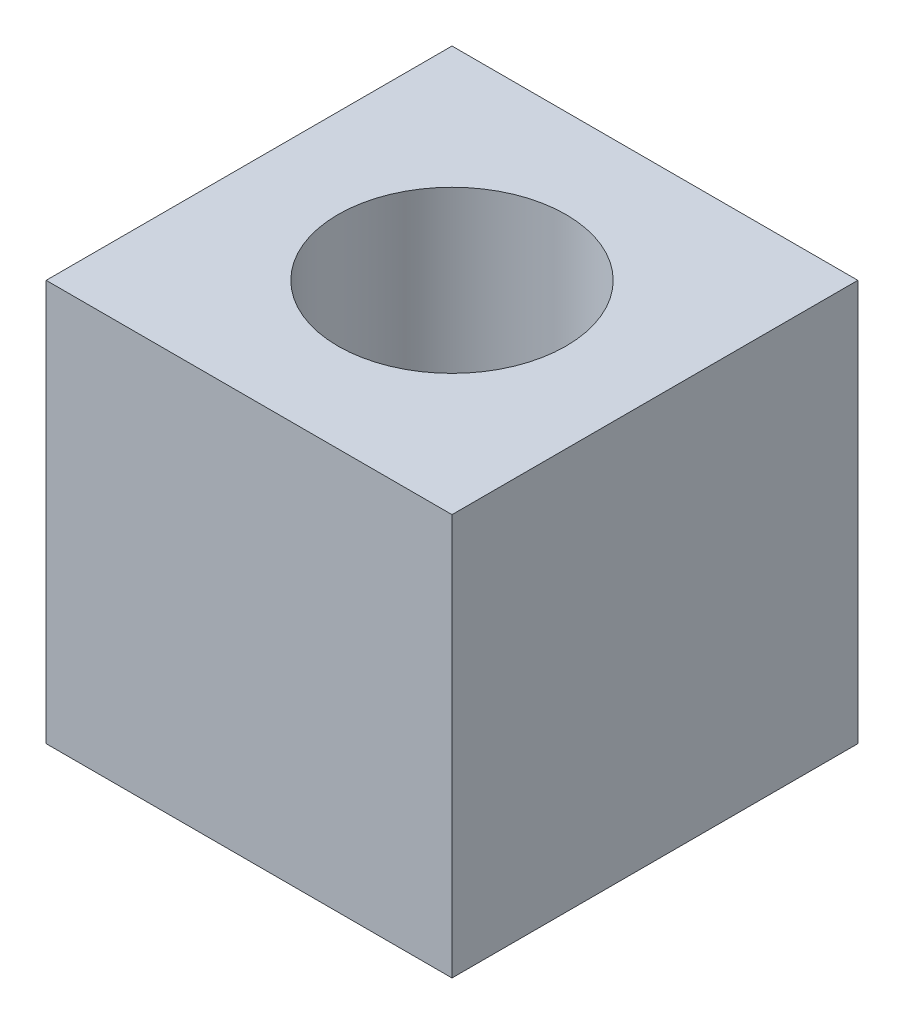
SolidWorks part; units mm, degrees
ref_plane "Front Plane" through (0, 0, 0) normal (0, 0, 1) x (1, 0, 0)
ref_plane "Top Plane" through (0, 0, 0) normal (0, 1, 0) x (1, 0, 0)
ref_plane "Right Plane" through (0, 0, 0) normal (1, 0, 0) x (0, 0, -1)
sketch "Sketch1" plane through (0, 0, 0) normal (0, 1, 0) x (1, 0, 0)
  line L0 (5.6515, 11.303) -> (5.6515, 0) construction
  line L1 (0, 0) -> (11.303, 0)
  line L2 (0, 0) -> (0, 11.303)
  line L3 (0, 11.303) -> (11.303, 11.303)
  line L4 (11.303, 0) -> (11.303, 11.303)
  line L5 (0, 5.6515) -> (11.303, 5.6515) construction
  circle A0 centre (5.6515, 5.6515) radius 3.175
  dimension "D3" = 6.35
  dimension "D1" = 11.303
  dimension "D2" = 11.303
extrude "Boss-Extrude1" add sketch "Sketch1" along normal blind 11.176
sketch "Sketch2" plane through (0, 11.176, 0) normal (0, 1, 0) x (1, 0, 0)
  circle A0 centre (5.6515, 5.6515) radius 3.175 construction
  circle A1 centre (5.6515, 5.6515) radius 3.175
  circle A2 centre (5.6515, 5.6515) radius 3.556
  dimension "D1" = 7.112
extrude "Cut-Extrude1" cut sketch "Sketch2" against normal up to next from offset 5.842
